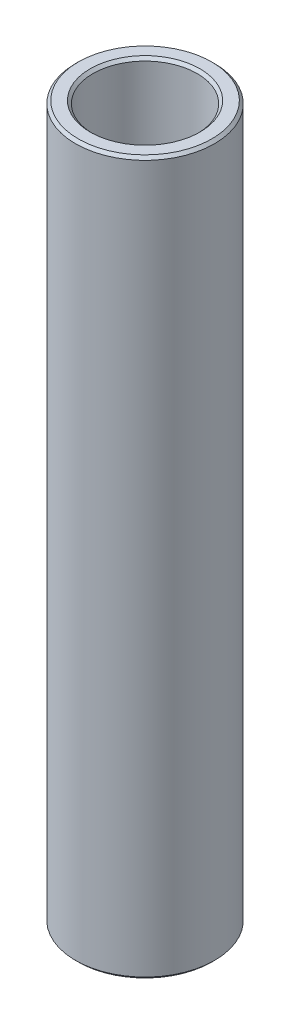
SolidWorks part; units mm, degrees
ref_plane "Front Plane" through (0, 0, 0) normal (0, 0, 1) x (1, 0, 0)
ref_plane "Top Plane" through (0, 0, 0) normal (0, 1, 0) x (1, 0, 0)
ref_plane "Right Plane" through (0, 0, 0) normal (1, 0, 0) x (0, 0, -1)
sketch "Sketch1" plane through (0, 0, 0) normal (0, 0, 1) x (1, 0, 0)
  line L0 (4.7625, 70.6437) -> (4.7625, 135.7791)
  line L1 (4.7625, 135.7791) -> (6.35, 135.7791)
  line L2 (6.35, 135.7791) -> (6.35, 70.6437)
  line L3 (6.35, 70.6437) -> (4.7625, 70.6437)
  line L4 (120.0875, 79.3749) -> (10.0875, 79.3749) construction
  line L6 (0, 61.1187) -> (0, 145.3041) construction
  dimension "D1" = 9.525
  dimension "D2" = 9.525
  dimension "D3" = 12.7
  dimension "D4" = 9.525
revolve "Revolve1" add sketch "Sketch1" angle 360 about L6
chamfer "Chamfer1" distance 0.254 angle 45 4 edges at (6.35, 135.7791, 0) (4.7625, 135.7791, 0) (4.7625, 70.6437, 0) (6.35, 70.6437, 0)
equation "\"D4@Sketch1\"=\"D1@Sketch1\""
